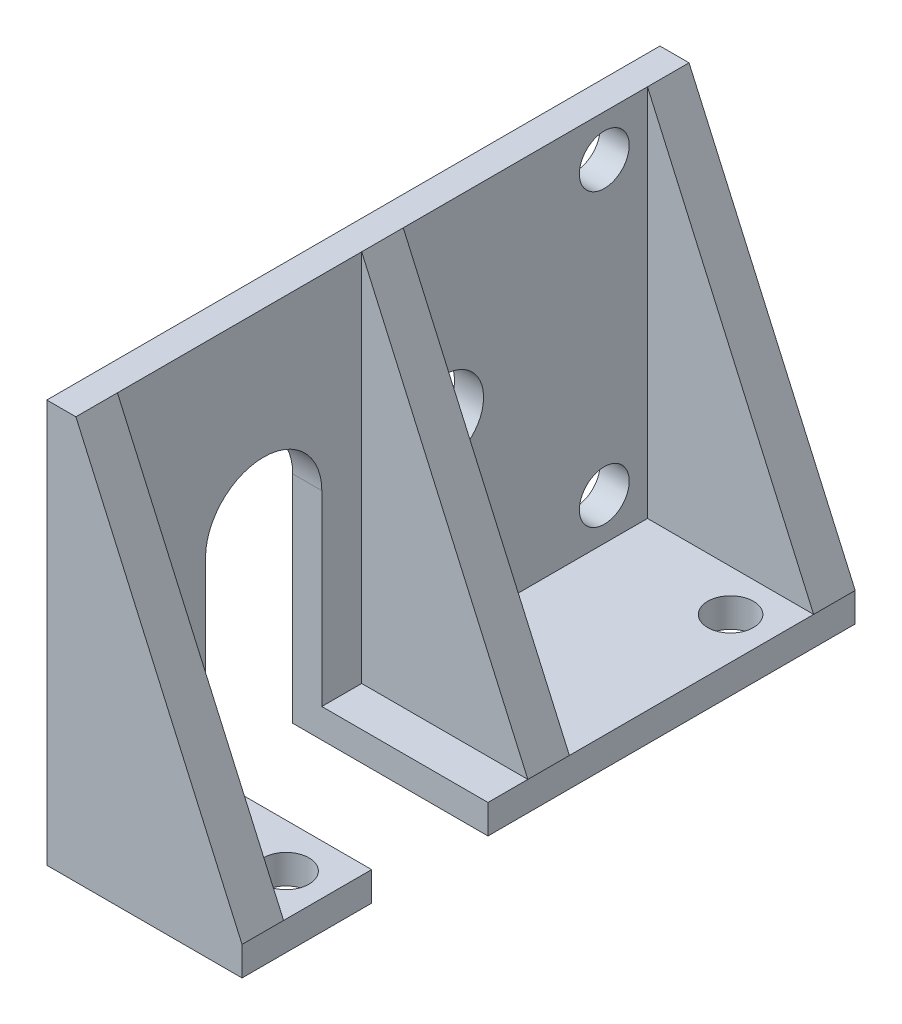
SolidWorks part; units mm, degrees
ref_plane "Front" through (0, 0, 0) normal (0, 0, 1) x (1, 0, 0)
ref_plane "Top" through (0, 0, 0) normal (0, 1, 0) x (1, 0, 0)
ref_plane "Right" through (0, 0, 0) normal (1, 0, 0) x (0, 0, -1)
sketch "Sketch1" plane through (0, 0, 0) normal (1, 0, 0) x (0, 0, -1)
  line L1 (0, 0) -> (36.9, 0)
  line L2 (0, 0) -> (0, 22.5)
  line L3 (0, 22.5) -> (36.9, 22.5)
  line L4 (36.9, 0) -> (36.9, 22.5)
  dimension "D1" = 36.9
  dimension "D2" = 22.5
extrude "basePlate" add sketch "Sketch1" along normal blind 1.75
sketch "Sketch2" plane through (0, 0, 0) normal (0, -1, 0) x (1, 0, 0)
  line L0 (1.75, -36.9) -> (0, -36.9) construction
  line L1 (0, 0) -> (11.75, 0)
  line L2 (0, 0) -> (0, -36.9)
  line L3 (0, -36.9) -> (11.75, -36.9)
  line L4 (11.75, 0) -> (11.75, -36.9)
  dimension "D1" = 11.75
extrude "Boss-Extrude2" add sketch "Sketch2" along normal blind 1.75
sketch "Sketch3" plane through (0, 0, 0) normal (0, 0, 1) x (1, 0, 0)
  line L0 (1.75, 22.5) -> (11.75, 0)
rib "support1" sketch "Sketch3" sketch "Sketch3" thickness 2.5 extrusion direction parallel to sketch draft on no parameters "D1"=2.5
ref_plane "referencePlane" through (0, 0, -18.45) normal (0, 0, 1) x (1, 0, 0)
mirror "support2" about plane through (0, 0, -18.45) normal (0, 0, 1) of "support1"
sketch "Sketch4" plane through (0, 0, -18.45) normal (0, 0, 1) x (1, 0, 0)
  line L0 (1.75, 22.5) -> (11.75, 0)
rib "support3" sketch "Sketch4" sketch "Sketch4" thickness 2.5 extrusion direction parallel to sketch draft on no parameters "D1"=2.5
sketch "Sketch5" plane through (1.75, 0, 0) normal (1, 0, 0) x (0, 0, -1)
  line L0 (18.45, -1.75) -> (18.45, 22.5) construction
  line L2 (36.9, -1.75) -> (0, -1.75) construction
  line L3 (19.7, 22.5) -> (17.2, 22.5) construction
  line L4 (36.9, 22.5) -> (36.9, 0) construction
  line L5 (34.4, 22.5) -> (19.7, 22.5) construction
  circle A2 centre (31.8, 2.5) radius 1.5
  circle A3 centre (31.8, 20) radius 1.5
  dimension "D1" = 17.5
  dimension "D4" = 3
  dimension "D2" = 5.1
  dimension "D3" = 2.5
extrude "motor_mountingHoles" cut sketch "Sketch5" against normal through all
sketch "Sketch7" plane through (11.75, 0, 0) normal (1, 0, 0) x (0, 0, -1)
  line L0 (36.9, -1.75) -> (36.9, 0) construction
  line L5 (36.9, -1.75) -> (0, -1.75) construction
  line L8 (18.45, -1.75) -> (18.45, 22.5) construction
  line L9 (19.7, 22.5) -> (17.2, 22.5) construction
  line L10 (7.8, -1.75) -> (7.8, 11.25)
  line L11 (14.8, -1.75) -> (7.8, -1.75)
  line L12 (14.8, -1.75) -> (14.8, 11.25)
  arc A1 (7.8, 11.25) -> (14.8, 11.25) centre (11.3, 11.25) cw
  dimension "D1" = 25.6
  dimension "D2" = 3.5
  dimension "D3" = 13
  dimension "D4" = 7
extrude "shaftSlot" cut sketch "Sketch7" against normal through all
sketch "Sketch8" plane through (0, 0, 0) normal (0, 1, 0) x (1, 0, 0)
  line L1 (1.75, 19.7) -> (1.75, 34.4) construction
  line L2 (11.75, 34.4) -> (11.75, 19.7) construction
  line L4 (11.75, 19.7) -> (1.75, 19.7) construction
  line L10 (11.75, 18.45) -> (0.8207, 18.45) construction
  line L11 (11.75, 19.7) -> (11.75, 17.2) construction
  line L12 (1.75, 34.4) -> (11.75, 34.4) construction
  line L13 (11.75, 7.8) -> (11.75, 2.5) construction
  line L14 (11.75, 7.8) -> (1.75, 7.8) construction
  circle A6 centre (9.25, 5.15) radius 1.375
  circle A7 centre (9.25, 31.9) radius 1.375
  circle A9 centre (4.25, 22.2) radius 1.375
  dimension "D1" = 2.5
  dimension "D8" = 2.5
  dimension "D6" = 2.75
  dimension "D2" = 2.5
  dimension "D3" = 2.5
  dimension "D4" = 2.5
  dimension "D5" = 2.65
extrude "chassis_mountingHoles" cut sketch "Sketch8" against normal through all
sketch "Sketch9" plane through (1.75, 0, 0) normal (1, 0, 0) x (0, 0, -1)
  line L0 (34.4, 22.5) -> (19.7, 22.5) construction
  line L1 (18.45, 22.5) -> (18.45, -1.75) construction
  line L2 (36.9, 22.5) -> (0, 22.5) construction
  line L3 (14.8, -1.75) -> (36.9, -1.75) construction
  circle A1 centre (22.185, 11.25) radius 2.35
  dimension "D1" = 4.7
  dimension "D2" = 3.735
  dimension "D3" = 11.25
extrude "indentHole" cut sketch "Sketch9" against normal blind 10
